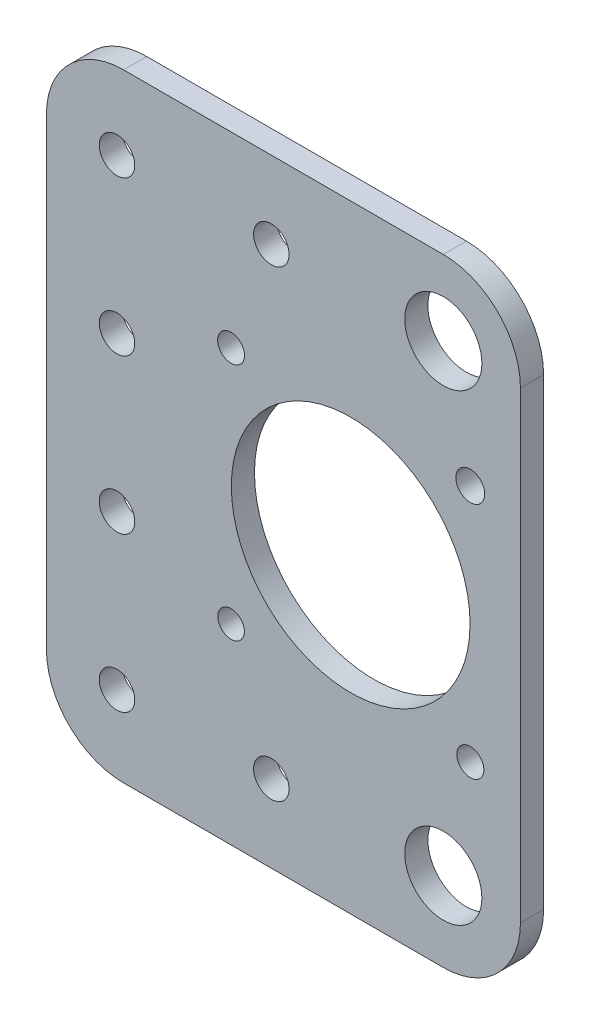
SolidWorks part; units mm, degrees
ref_plane "Front Plane" through (0, 0, 0) normal (0, 0, 1) x (1, 0, 0)
ref_plane "Top Plane" through (0, 0, 0) normal (0, 1, 0) x (1, 0, 0)
ref_plane "Right Plane" through (0, 0, 0) normal (1, 0, 0) x (0, 0, -1)
sketch "Sketch1" plane through (0, 0, 0) normal (0, 0, 1) x (1, 0, 0)
  line L1 (116.5258, -71.8662) -> (157.9607, -71.8662)
  line L2 (106.5258, -81.8662) -> (106.5258, -141.8968)
  line L3 (116.5258, -151.8968) -> (157.9607, -151.8968)
  line L4 (167.9607, -81.8662) -> (167.9607, -141.8968)
  line L5 (145.9607, -111.5917) -> (157.9607, -111.5917) construction
  line L6 (157.9607, -111.5917) -> (157.9607, -81.5917) construction
  line L7 (157.9607, -111.5917) -> (157.9607, -141.5917) construction
  circle A0 centre (115.6746, -101.8662) radius 2.3
  circle A1 centre (115.6746, -121.8662) radius 2.3
  circle A2 centre (135.6746, -141.8662) radius 2.3
  circle A3 centre (135.6746, -81.8662) radius 2.3
  circle A4 centre (115.6746, -81.8662) radius 2.3
  circle A5 centre (115.6746, -141.8662) radius 2.3
  circle A6 centre (130.4607, -96.0917) radius 1.7379
  circle A7 centre (161.4607, -96.0917) radius 1.8732
  circle A8 centre (130.4607, -127.0917) radius 1.7223
  circle A9 centre (161.4607, -127.0917) radius 1.7542
  circle A10 centre (145.9607, -111.5917) radius 15.4696
  arc A11 (157.9607, -151.8968) -> (167.9607, -141.8968) centre (157.9607, -141.8968) ccw
  arc A12 (157.9607, -71.8662) -> (167.9607, -81.8662) centre (157.9607, -81.8662) cw
  arc A13 (106.5258, -141.8968) -> (116.5258, -151.8968) centre (116.5258, -141.8968) ccw
  arc A14 (116.5258, -71.8662) -> (106.5258, -81.8662) centre (116.5258, -81.8662) ccw
  circle A15 centre (157.9607, -81.5917) radius 5
  circle A16 centre (157.9607, -141.5917) radius 5
  point P47 (106.5258, -71.8662)
  dimension "D1" = 10
  dimension "D4" = 12
  dimension "D2" = 30
  dimension "D3" = 30
extrude "Boss-Extrude1" add sketch "Sketch1" along normal blind 3
